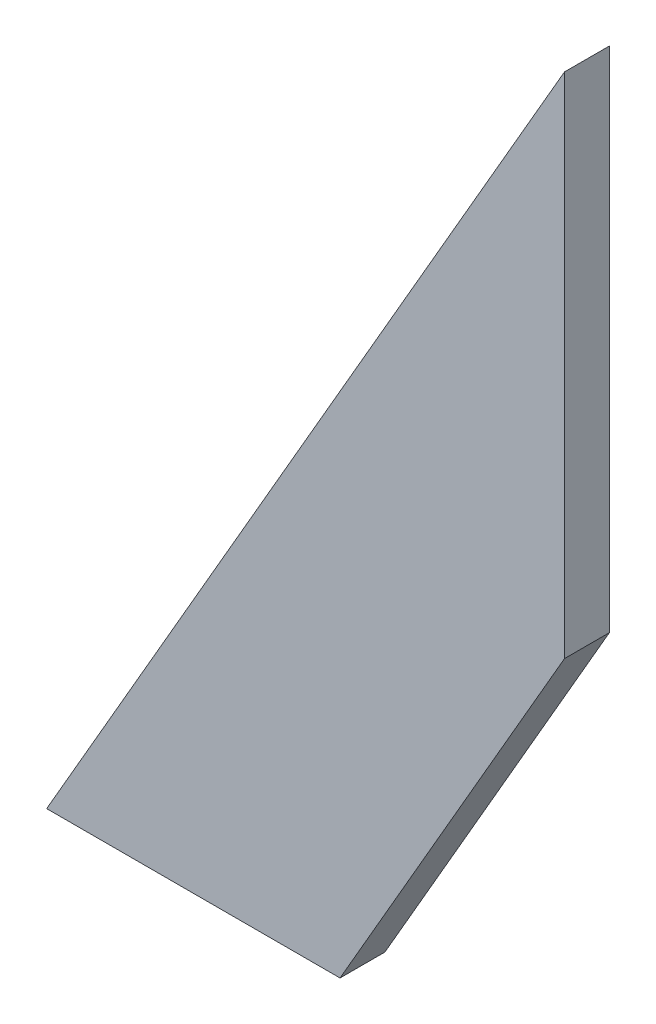
SolidWorks part; units mm, degrees
ref_plane "Front Plane" through (0, 0, 0) normal (0, 0, 1) x (1, 0, 0)
ref_plane "Top Plane" through (0, 0, 0) normal (0, 1, 0) x (1, 0, 0)
ref_plane "Right Plane" through (0, 0, 0) normal (1, 0, 0) x (0, 0, -1)
sketch "Sketch1" plane through (0, 0, 0) normal (0, 0, 1) x (1, 0, 0)
  line L0 (-258.6568, 260.5568) -> (-258.6568, 226.5622)
  line L2 (-258.6568, 226.5622) -> (-273.676, 200.5453)
  line L4 (-273.676, 200.5453) -> (-293.3044, 200.5453)
  line L5 (-293.3044, 200.5453) -> (-258.6568, 260.5568)
extrude "Boss-Extrude1" add sketch "Sketch1" along normal blind 3
